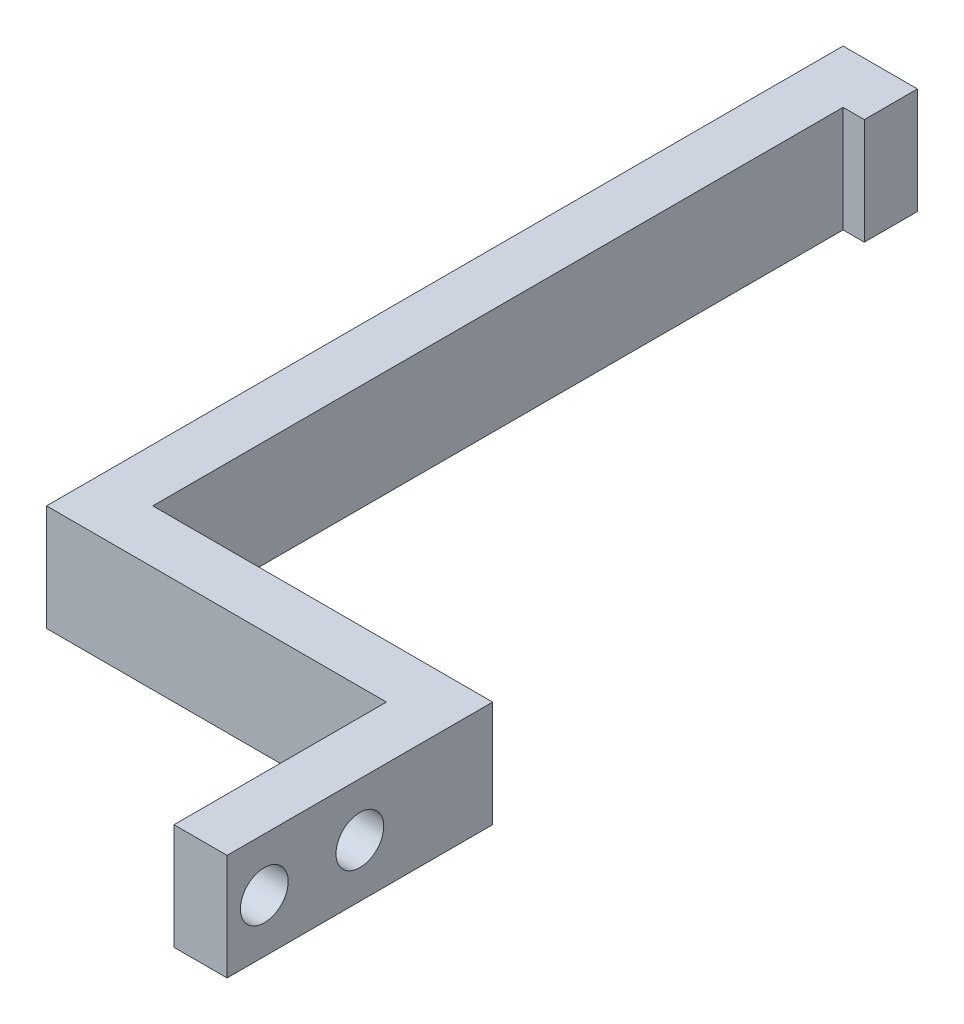
SolidWorks part; units mm, degrees
material "100MnCrW4"
ref_plane "Front Plane" through (0, 0, 0) normal (0, 0, 1) x (1, 0, 0)
ref_plane "Top Plane" through (0, 0, 0) normal (0, 1, 0) x (1, 0, 0)
ref_plane "Right Plane" through (0, 0, 0) normal (1, 0, 0) x (0, 0, -1)
sketch "Sketch2" plane through (0, 0, 0) normal (0, 1, 0) x (1, 0, 0)
  line L0 (0, 0) -> (0, 25)
  line L1 (0, 25) -> (-32, 25)
  line L2 (-32, 25) -> (-32, 95)
  line L3 (-32, 95) -> (-37, 95)
  line L4 (-37, 95) -> (-37, 20)
  line L5 (-37, 20) -> (-5, 20)
  line L6 (-5, 20) -> (-5, 0)
  line L7 (-5, 0) -> (0, 0)
  line L8 (-32, 95) -> (-30, 95)
  line L9 (-30, 95) -> (-30, 90)
  line L10 (-30, 90) -> (-32, 90)
  dimension "D7" = 5
  dimension "D6" = 5
  dimension "D1" = 25
  dimension "D2" = 5
  dimension "D3" = 70
  dimension "D4" = 5
  dimension "D5" = 37
  dimension "D8" = 2
extrude "Boss-Extrude1" add sketch "Sketch2" along normal blind 10
sketch "Sketch3" plane through (0, 0, 0) normal (1, 0, 0) x (0, 0, -1)
  line L0 (0, 10) -> (0, 0) construction
  circle A0 centre (3.5, 5) radius 2.25
  circle A1 centre (12.5, 5) radius 2.25
  point P8 (0, 5)
  dimension "D1" = 4.5
  dimension "D2" = 9
  dimension "D3" = 3.5
extrude "Cut-Extrude1" cut sketch "Sketch3" against normal through all
